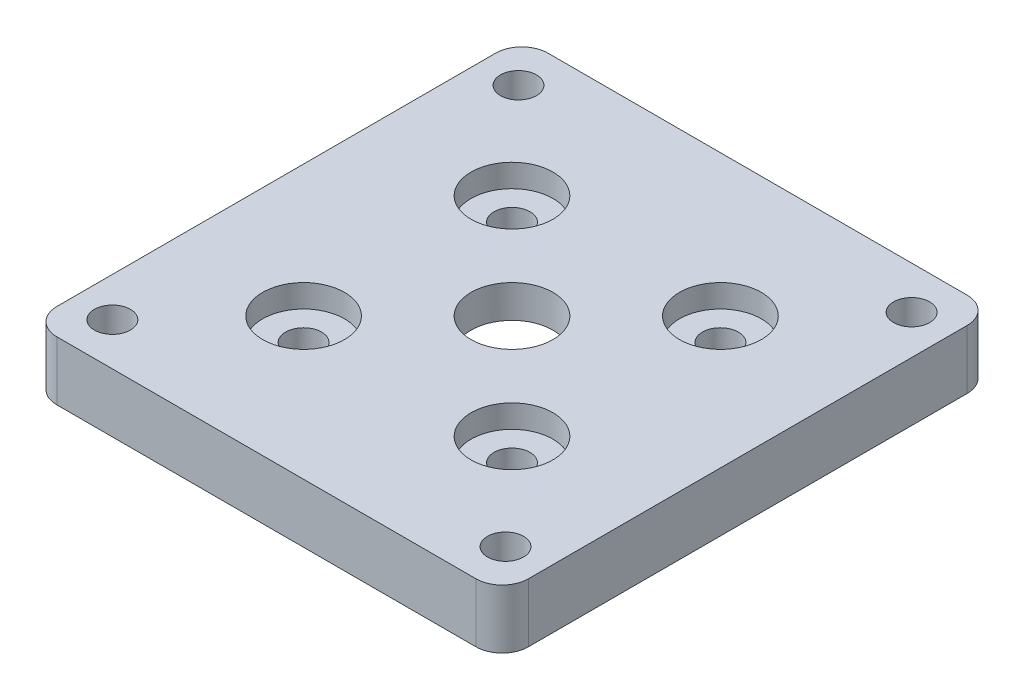
SolidWorks part; units mm, degrees
ref_plane "Front Plane" through (0, 0, 0) normal (0, 0, 1) x (1, 0, 0)
ref_plane "Top Plane" through (0, 0, 0) normal (0, 1, 0) x (1, 0, 0)
ref_plane "Right Plane" through (0, 0, 0) normal (1, 0, 0) x (0, 0, -1)
sketch "Sketch1" plane through (0, 0, 0) normal (0, 1, 0) x (1, 0, 0)
  line L0 (0, 0) -> (60.02, 0)
  line L1 (0, 0) -> (0, -62)
  line L2 (0, -62) -> (60.02, -62)
  line L3 (60.02, -62) -> (60.02, 0)
  line L9 (-5.99, 6.5) -> (66.01, 6.5)
  line L10 (-5.99, 6.5) -> (-5.99, -68.5)
  line L11 (-5.99, -68.5) -> (66.01, -68.5)
  line L12 (66.01, 6.5) -> (66.01, -68.5)
  circle A4 centre (0, 0) radius 2.75
  circle A5 centre (60.02, 0) radius 2.75
  circle A6 centre (60.02, -62) radius 2.75
  circle A7 centre (0, -62) radius 2.75
  circle A8 centre (30.01, -31) radius 6.25
  circle A9 centre (30.01, -31) radius 22.5
  circle A10 centre (14.1001, -15.0901) radius 2.75
  circle A11 centre (14.1001, -46.9099) radius 2.75
  circle A12 centre (45.9199, -46.9099) radius 2.75
  circle A13 centre (45.9199, -15.0901) radius 2.75
  dimension "D7" = 75
  dimension "D2" = 60.02
  dimension "D6" = 62
  dimension "D8" = 72
  dimension "D9" = 5.99
  dimension "D10" = 6.5
extrude "Boss-Extrude3" add sketch "Sketch1" along normal blind 9
sketch "Sketch3" plane through (0, 9, 0) normal (0, 1, 0) x (1, 0, 0)
  circle A1 centre (14.1001, -46.9099) radius 6.25
  circle A4 centre (14.1001, -15.0901) radius 6.25
  circle A5 centre (45.9199, -15.0901) radius 6.25
  circle A6 centre (45.9199, -46.9099) radius 6.25
fillet "Fillet1" radius 4 4 edges at (-5.99, 4.5, 68.5) (66.01, 4.5, 68.5) (66.01, 4.5, -6.5) (-5.99, 4.5, -6.5)
sketch "Sketch4" plane through (0, 0, 0) normal (0, -1, 0) x (1, 0, 0)
  circle A0 centre (30.01, 31) radius 16.25
extrude "Cut-Extrude2" cut sketch "Sketch4" against normal blind 4
extrude "Cut-Extrude3" cut sketch "Sketch3" against normal blind 3.5
